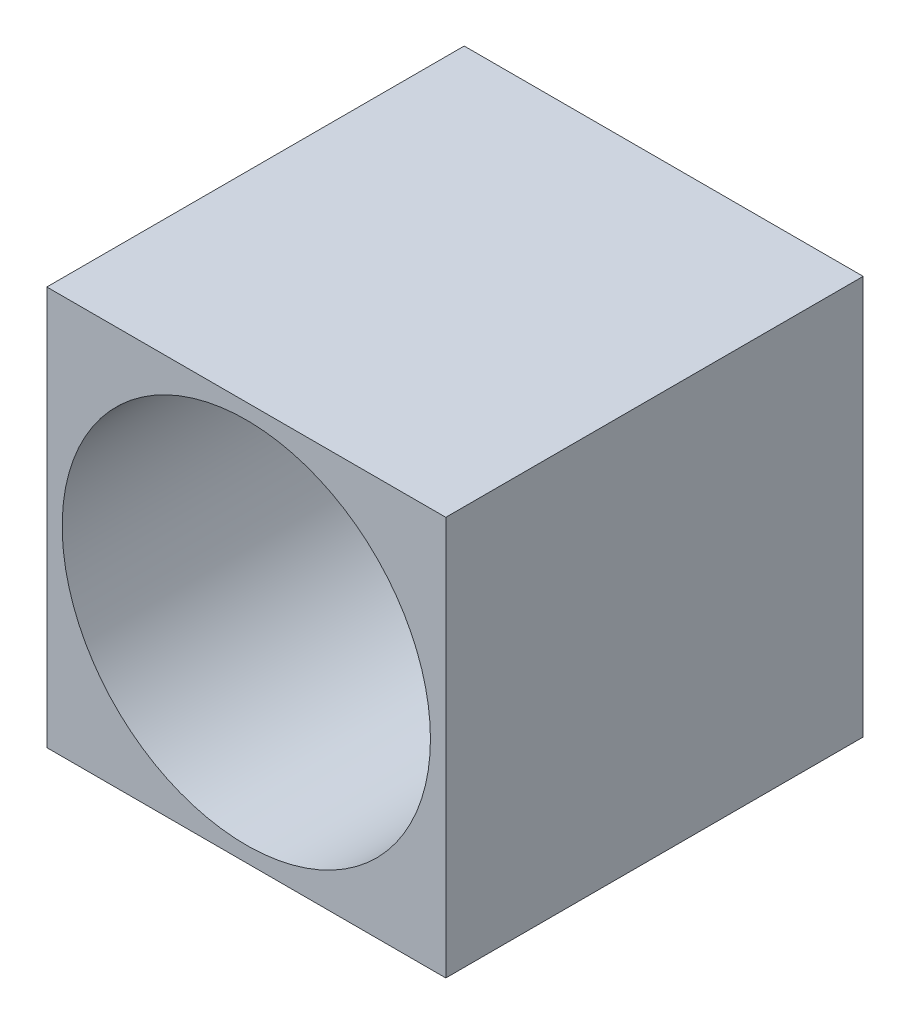
SolidWorks part; units mm, degrees
material "Commercial Bronze, UNS C22000 (90-10 Bronze)"
ref_plane "Front Plane" through (0, 0, 0) normal (0, 0, 1) x (1, 0, 0)
ref_plane "Top Plane" through (0, 0, 0) normal (0, 1, 0) x (1, 0, 0)
ref_plane "Right Plane" through (0, 0, 0) normal (1, 0, 0) x (0, 0, -1)
ref_plane "Plane1" through (0, 0, 0) normal (0, 0, -1) x (-1, 0, 0)
sketch "Sketch1" plane through (0, 0, 0) normal (0, 0, -1) x (-1, 0, 0)
  line L0 (-1.625, 1.625) -> (-1.625, -1.625)
  line L1 (-1.625, -1.625) -> (1.625, -1.625)
  line L2 (1.625, -1.625) -> (1.625, 1.625)
  line L3 (1.625, 1.625) -> (-1.625, 1.625)
  circle A0 centre (0, 0) radius 1.5
extrude "Boss-Extrude1" add sketch "Sketch1" against normal blind 3.4
